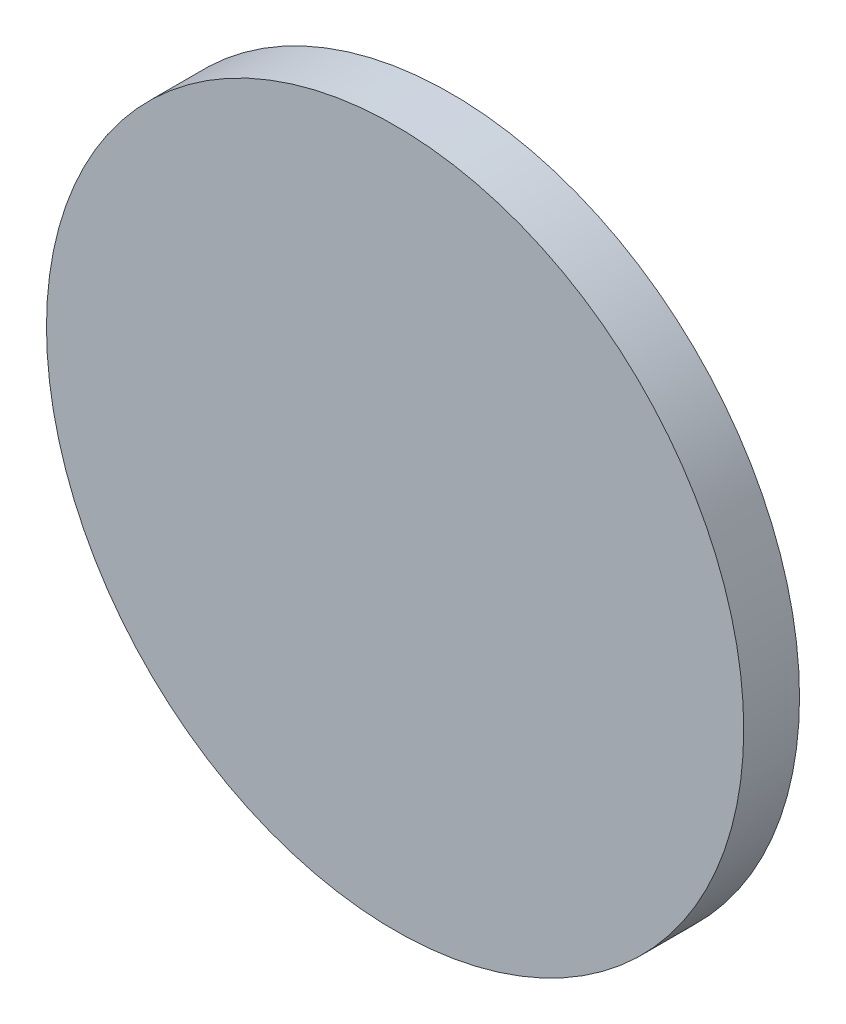
SolidWorks part; units mm, degrees
ref_plane "前视基准面" through (0, 0, 0) normal (0, 0, 1) x (1, 0, 0)
ref_plane "上视基准面" through (0, 0, 0) normal (0, 1, 0) x (1, 0, 0)
ref_plane "右视基准面" through (0, 0, 0) normal (1, 0, 0) x (0, 0, -1)
sketch "草图1" plane through (0, 0, 0) normal (0, 0, 1) x (1, 0, 0)
  circle A0 centre (0, 0) radius 6.25
  dimension "D1" = 12.5
extrude "凸台-拉伸1" add sketch "草图1" along normal blind 1 contours A0
